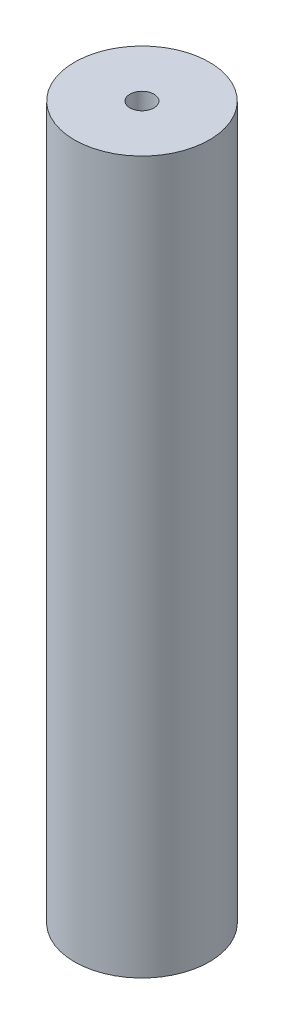
SolidWorks part; units mm, degrees
ref_plane "Front Plane" through (0, 0, 0) normal (0, 0, 1) x (1, 0, 0)
ref_plane "Top Plane" through (0, 0, 0) normal (0, 1, 0) x (1, 0, 0)
ref_plane "Right Plane" through (0, 0, 0) normal (1, 0, 0) x (0, 0, -1)
sketch "Sketch1" plane through (0, 0, 0) normal (0, 1, 0) x (1, 0, 0)
  circle A0 centre (0, 0) radius 6.35
  circle A1 centre (0, 0) radius 1.1303
  dimension "D1" = 12.7
  dimension "D2" = 2.2606
extrude "Boss-Extrude1" add sketch "Sketch1" along normal blind 67.056
